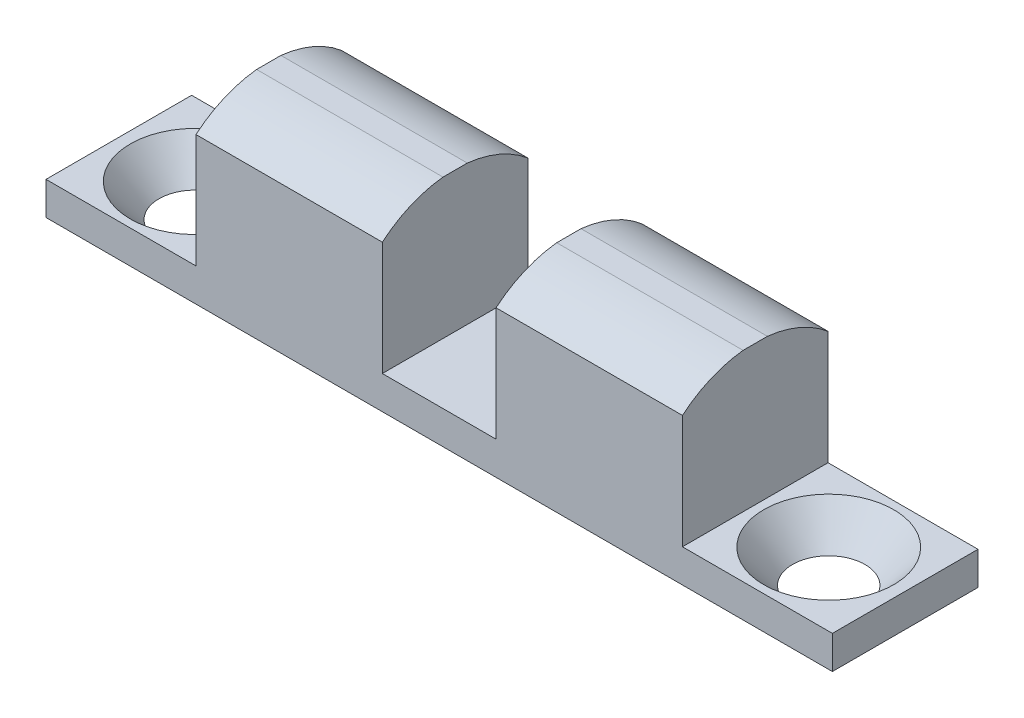
SolidWorks part; units mm, degrees
ref_plane "Front Plane" through (0, 0, 0) normal (0, 0, 1) x (1, 0, 0)
ref_plane "Top Plane" through (0, 0, 0) normal (0, 1, 0) x (1, 0, 0)
ref_plane "Right Plane" through (0, 0, 0) normal (1, 0, 0) x (0, 0, -1)
sketch "Sketch2" plane through (0, 0, 0) normal (0, 1, 0) x (1, 0, 0)
  line L1 (-43.1557, -7.3508) -> (-0.2932, -7.3508)
  line L2 (-43.1557, -7.3508) -> (-43.1557, -15.2883)
  line L3 (-43.1557, -15.2883) -> (-0.2932, -15.2883)
  line L4 (-0.2932, -7.3508) -> (-0.2932, -15.2883)
  dimension "D1" = 7.9375
  dimension "D2" = 42.8625
extrude "Boss-Extrude1" add sketch "Sketch2" along normal blind 1.8034
sketch "Sketch3" plane through (0, 1.8034, 0) normal (0, 1, 0) x (1, 0, 0)
  line L0 (-0.2932, -7.3508) -> (-43.1557, -7.3508) construction
  line L1 (-34.9832, -7.3508) -> (-24.8232, -7.3508)
  line L2 (-34.9832, -7.3508) -> (-34.9832, -15.2883)
  line L3 (-34.9832, -15.2883) -> (-24.8232, -15.2883)
  line L4 (-24.8232, -7.3508) -> (-24.8232, -15.2883)
  line L5 (-43.1557, -15.2883) -> (-0.2932, -15.2883) construction
  line L6 (-18.6256, -7.3508) -> (-18.6256, -15.2883)
  line L7 (-18.6256, -7.3508) -> (-8.4656, -7.3508)
  line L8 (-8.4656, -7.3508) -> (-8.4656, -15.2883)
  line L9 (-18.6256, -15.2883) -> (-8.4656, -15.2883)
  line L10 (-43.1557, -7.3508) -> (-43.1557, -15.2883) construction
  dimension "D2" = 10.16
  dimension "D3" = 26.5176
  dimension "D4" = 8.1724
  dimension "D1" = 2
extrude "Boss-Extrude2" add sketch "Sketch3" along normal blind 7.62
sketch "Sketch5" plane through (-34.9832, 0, 0) normal (-1, 0, 0) x (0, 0, 1)
  line L0 (7.3508, 9.4234) -> (7.3508, 1.8034) construction
  line L1 (15.2883, 9.4234) -> (15.2883, 1.8034) construction
  line L2 (7.3508, 8.0057) -> (7.3508, 10.1178)
  line L3 (7.3508, 10.1178) -> (15.2883, 10.1178)
  line L4 (15.2883, 10.1178) -> (15.2883, 8.0057)
  arc A0 (7.3508, 8.0057) -> (15.2883, 8.0057) centre (11.3196, 3.3141) cw
extrude "Cut-Extrude1" cut sketch "Sketch5" against normal through all
hole_wizard "CSK for #6 Flat Head Machine Screw1" positions "Sketch7" profile "Sketch6" countersink size "#6" standard "Ansi Inch" end condition through all
sketch "Sketch7" plane through (0, 1.8034, 0) normal (0, 1, 0) x (-1, 0, 0)
  line L0 (0.2932, 15.2883) -> (0.2932, 7.3508) construction
  line L1 (8.4656, 15.2883) -> (0.2932, 15.2883) construction
  line L2 (43.1557, 15.2883) -> (34.9832, 15.2883) construction
  point P0 (4.4604, 11.3196)
  point P1 (38.9885, 11.3204)
  point P9 (39.0694, 15.2883)
  dimension "D1" = 34.5281
  dimension "D2" = 4.1672
  dimension "D3" = 3.9688
  dimension "D4" = 3.9688
sketch "Sketch6" plane through (-4.4604, 1.8034, 11.3196) normal (1, 0, 0) x (0, 0, 1)
  line L0 (0, 0) -> (0, 1.8034)
  line L1 (0, 1.8034) -> (1.8986, 1.8034)
  line L2 (1.8986, 1.8034) -> (1.8986, 1.892)
  line L3 (1.8986, 1.892) -> (3.5433, 0)
  line L5 (3.5433, 0) -> (0, 0)
  line L6 (-1.8987, 1.892) -> (-3.5433, 0) construction
  line L11 (0, -6.35) -> (0, 107.95) construction
  dimension "Thru Hole Dia." = 3.7973
  dimension "Thru Hole Depth" = 1.8034
  dimension "Near C'Sink Dia." = 7.0866
  dimension "Near C'Sink Angle" = 82
equation "\"D4@Sketch3\" = (\"D2@Sketch2\"-\"D3@Sketch3\")/2"
equation "\"D2@Sketch7\" = (\"D2@Sketch2\"-\"D1@Sketch7\")/2"
equation "\"D3@Sketch7\" = \"D1@Sketch2\"/2"
equation "\"D4@Sketch7\" = \"D3@Sketch7\""
